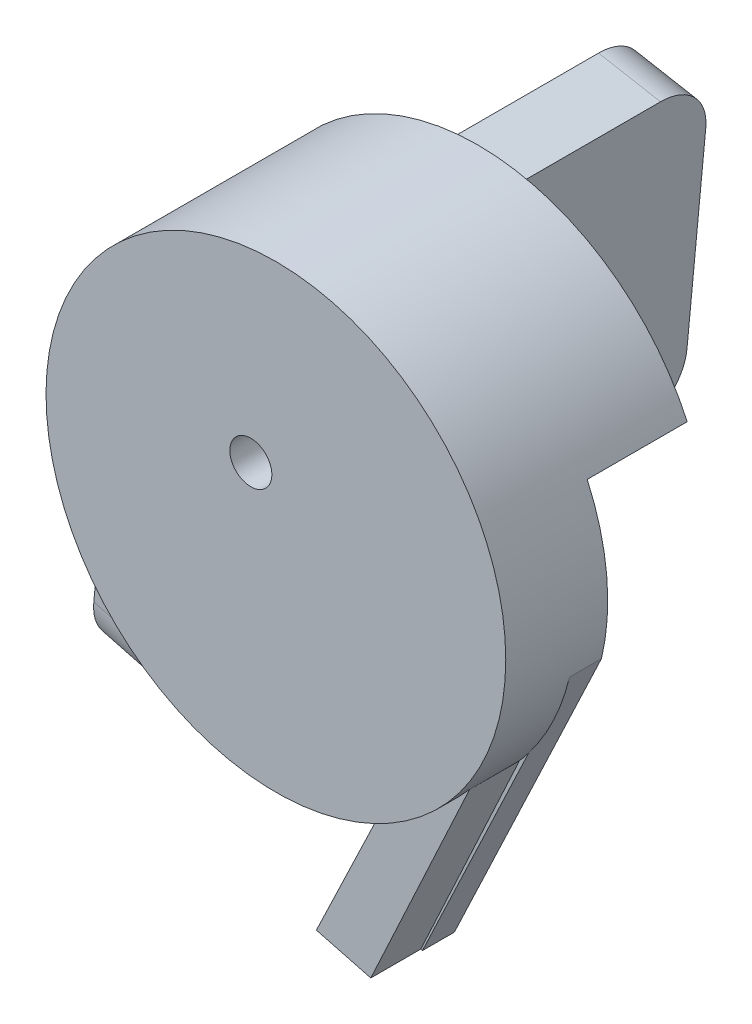
SolidWorks part; units mm, degrees
ref_plane "Front Plane" through (0, 0, 0) normal (0, 0, 1) x (1, 0, 0)
ref_plane "Top Plane" through (0, 0, 0) normal (0, 1, 0) x (1, 0, 0)
ref_plane "Right Plane" through (0, 0, 0) normal (1, 0, 0) x (0, 0, -1)
sketch "Sketch1" plane through (0, 0, 0) normal (0, 0, 1) x (1, 0, 0)
  line L0 (-16.7339, 0.7347) -> (-19.5437, -29.2653)
  line L1 (-19.5437, -29.2653) -> (1.9856, -34.8971)
  line L2 (1.9856, -34.8971) -> (14.8304, -7.786)
  line L3 (0.192, -0.8506) -> (14.8304, -7.786)
  line L4 (-16.7339, 0.7347) -> (0.192, -0.8506)
  line L5 (-22.9127, 2.0023) -> (-25.6907, -27.6574)
  line L6 (-25.6907, -27.6574) -> (7.6604, -36.3816)
  line L7 (7.6604, -36.3816) -> (22.3757, -5.3225)
  circle A0 centre (0, 0) radius 16.75
  circle A1 centre (0, 0) radius 23
  dimension "D2" = 33.5
  dimension "D12" = 0
  dimension "D13" = 46
  dimension "D1" = 0
  dimension "D3" = 16.75
  dimension "D4" = 16.75
  dimension "D5" = 0
  dimension "D6" = 30
  dimension "D7" = 90
  dimension "D10" = 90
  dimension "D11" = 30
  dimension "D14" = 23
  dimension "D15" = 23
  dimension "D16" = 180
  dimension "D17" = 180
  dimension "D19" = 160
extrude "Boss-Extrude3" add sketch "Sketch1" along normal blind 13.2 contours A1 L5 L6 L0 | A1 L0 A0 L2 L7 | A1 L2 L6 L7
sketch "Sketch2" plane through (0, 0, 0) normal (0, 0, -1) x (-1, 0, 0)
  line L0 (22.9127, 2.0023) -> (16.7206, 0.8761)
  line L1 (16.7206, 0.8761) -> (19.5437, -29.2653)
  line L2 (19.5437, -29.2653) -> (25.6907, -27.6574)
  line L3 (25.6907, -27.6574) -> (22.9127, 2.0023)
  line L4 (16.7339, 0.7347) -> (19.5437, -29.2653) construction
  line L5 (22.9127, 2.0023) -> (25.6907, -27.6574) construction
  line L7 (25.6907, -27.6574) -> (19.5437, -29.2653) construction
  point P4 (24.3017, -12.8275)
  point P11 (18.1388, -14.2653)
  dimension "D1" = 0
  dimension "D2" = 0
  dimension "D3" = 180
  dimension "D4" = 0
  dimension "D5" = 0
  dimension "D6" = 0
extrude "Boss-Extrude4" add sketch "Sketch2" along normal blind 40
sketch "Sketch3" plane through (0, 0, 13.2) normal (0, 0, 1) x (1, 0, 0)
  circle A0 centre (0, 0) radius 23
  arc A1 (14.8304, -7.786) -> (-16.7339, 0.7347) centre (0, 0) ccw construction
  dimension "D2" = 46
  dimension "D1" = 0
extrude "Boss-Extrude5" add sketch "Sketch3" along normal blind 7
sketch "Sketch4" plane through (0, 0, 20.2) normal (0, 0, 1) x (1, 0, 0)
  circle A0 centre (-2.506, 4.3267) radius 2.1017
  circle A2 centre (0, 0) radius 23 construction
  dimension "D1" = 5
extrude "Cut-Extrude1" cut sketch "Sketch4" against normal blind 10
sketch "Sketch6" plane through (0, 0, 0) normal (0, 0, -1) x (-1, 0, 0)
  line L1 (-26.1892, 9.4902) -> (-0.4743, 9.4902)
  line L2 (-26.1892, 9.4902) -> (-26.1892, -44.4369)
  line L3 (-26.1892, -44.4369) -> (-0.4743, -44.4369)
  line L4 (-0.4743, 9.4902) -> (-0.4743, -44.4369)
extrude "Cut-Extrude2" cut sketch "Sketch6" against normal blind 10
sketch "Sketch7" plane through (0, 0, 13.2) normal (0, 0, 1) x (1, 0, 0)
  line L0 (2.0506, -34.9141) -> (7.4943, -36.3381)
  line L1 (7.4943, -36.3381) -> (17.7899, -14.1801)
  line L2 (17.7899, -14.1801) -> (12.5045, -13.1112)
  line L3 (12.5045, -13.1112) -> (2.0506, -34.9141)
  line L4 (1.9856, -34.8971) -> (7.6604, -36.3816) construction
  arc M1 (18.2907, -13.9445) -> (8.3693, -21.4232) centre (0, 0) cw
  line M3 (1.9856, -34.8971) -> (7.6604, -36.3816)
  dimension "D1" = 180
  dimension "D2" = 0
extrude "Boss-Extrude6" add sketch "Sketch7" along normal blind 5 contours L3 L1 M1 M3
sketch "Sketch8" plane through (-16.6566, 1.5601, 0) normal (0.9956, -0.0933, 0) x (0, 0, -1)
  line L0 (-13.2, -0.829) -> (-13.2, -15.7837) construction
  line L1 (28.8, -8.5) -> (13.8, -8.5)
  line L2 (28.8, -8.5) -> (28.8, -16.5)
  line L3 (28.8, -16.5) -> (13.8, -16.5)
  line L4 (13.8, -8.5) -> (13.8, -16.5)
  line L5 (0, 23) -> (-20.2, 23) construction
  line L6 (14.6914, -16.5) -> (10.6914, -16.5)
  line L7 (10.6914, -16.5) -> (13.8, -8.5)
  line L8 (11.5362, -16.5) -> (11.3479, -14.8105)
  dimension "D1" = 27
  dimension "D2" = 8
  dimension "D3" = 31.5
  dimension "D4" = 0
  dimension "D5" = 0
  dimension "D6" = 4
  dimension "D7" = 180
  dimension "D8" = 0
  dimension "D9" = 0
  dimension "D10" = 1.7
  dimension "D11" = 15
sketch "Sketch11" plane through (-22.8993, 2.1448, 0) normal (-0.9956, 0.0933, 0) x (0, 0, 1)
  text T0 "GIAU-QUANG" font "Century Gothic" height in points 15
extrude "Cut-Extrude5" cut sketch "Sketch11" against normal blind 5
fillet "Fillet5" radius 5 1 edges at (-22.6172, -28.4613, -40)
fillet "Fillet6" radius 5 1 edges at (-19.8167, 1.4392, -40)
fillet "Fillet7" radius 5 1 edges at (-22.6172, -28.4613, 13.2)
